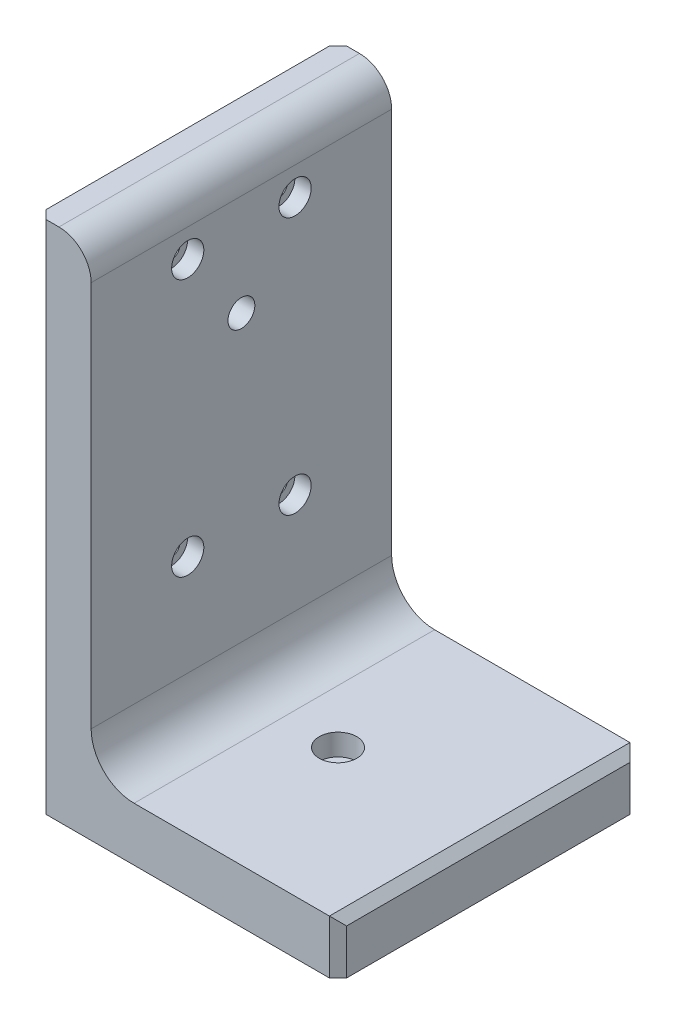
SolidWorks part; units mm, degrees
ref_plane "Plane1" through (0, 0, 0) normal (0, 0, 1) x (1, 0, 0)
ref_plane "Plane2" through (0, 0, 0) normal (0, 1, 0) x (1, 0, 0)
ref_plane "Plane3" through (0, 0, 0) normal (1, 0, 0) x (0, 0, -1)
extrude "BaseSteelAngle" add sketch "Sketch1" along normal mid plane 88.9
sketch "Sketch1" plane through (0, 0, 0) normal (0, 0, 1) x (1, 0, 0)
  line L0 (0, 0) -> (0, 152.4)
  line L1 (0, 152.4) -> (6.3551, 152.4)
  line L2 (15.875, 142.8801) -> (15.875, 28.575)
  line L3 (28.575, 15.875) -> (142.8801, 15.875)
  line L4 (152.4, 6.3551) -> (152.4, 0)
  line L5 (152.4, 0) -> (0, 0)
  arc A0 (152.4, 6.3551) -> (142.8801, 15.875) centre (142.8801, 6.3551) ccw
  arc A1 (6.3551, 152.4) -> (15.875, 142.8801) centre (6.3551, 142.8801) cw
  arc A2 (28.575, 15.875) -> (15.875, 28.575) centre (28.575, 28.575) cw
  circle A3 centre (0, 0) radius 9.525 construction
  dimension "D2" = 6.3551
  dimension "Radius_1" = 12.7
  dimension "Radius_2" = 9.525
  dimension "D1" = 15.875
  dimension "V_leg" = 152.4
  dimension "H_leg" = 152.4
  dimension "Thickness" = 15.875
  dimension "Flat_wid" = 6.3551
hole_wizard "#10-32 Tapped Hole1" positions "Sketch3" profile "Sketch2" tap size "#10-32" standard "Ansi Inch"
sketch "Sketch3" plane through (15.875, 0, 0) normal (1, 0, 0) x (0, 0, -1)
  point P0 (20.6375, 70.9295)
  point P1 (-20.6375, 70.9295)
  point P4 (-20.6375, 140.7795)
  point P7 (20.6375, 140.7795)
sketch "Sketch2" plane through (15.875, 70.9295, -20.6375) normal (0, 1, 0) x (0, 0, -1)
  line L0 (0, 0) -> (0, 15.875)
  line L1 (0, 15.875) -> (2.0193, 15.875)
  line L2 (2.0193, 15.875) -> (2.0193, 0)
  line L5 (2.0193, 0) -> (0, 0)
  line L11 (0, -6.35) -> (0, 107.95) construction
  dimension "Thru Tap Drill Dia." = 4.0386
  dimension "Thru Tap Drill Depth" = 15.875
cosmetic thread "Hole Thread1" [suppressed] parameters "D2"=4.826
cosmetic thread "Hole Thread2" [suppressed] parameters "D2"=4.826
cosmetic thread "Hole Thread3" [suppressed] parameters "D2"=4.826
cosmetic thread "Hole Thread4" [suppressed] parameters "D2"=4.826
hole_wizard "#10-32 Tapped Hole2" positions "Sketch5" profile "Sketch4" tap size "#10-32" standard "Ansi Inch"
sketch "Sketch5" plane through (0, 0, 0) normal (-1, 0, 0) x (0, 0, 1)
  point P0 (0, 7.9375)
  point P1 (0, 93.6625)
  dimension "D1" = 85.725
cosmetic thread "Hole Thread5" [suppressed] parameters "D1"=12.7, "D2"=4.826
cosmetic thread "Hole Thread6" [suppressed] parameters "D1"=12.7, "D2"=4.826
sketch "Sketch4" plane through (0, 7.9375, 0) normal (0, 1, 0) x (0, 0, 1)
  line L0 (0, 0) -> (0, 17.8757)
  line L1 (0, 17.8757) -> (2.0193, 16.6624)
  line L2 (2.0193, 16.6624) -> (2.0193, 0)
  line L5 (2.0193, 0) -> (0, 0)
  line L10 (0, 17.8757) -> (-2.0193, 16.6624) construction
  line L11 (0, -6.35) -> (0, 107.95) construction
  dimension "Tap Drill Dia." = 4.0386
  dimension "Tap Drill Depth" = 16.6624
  dimension "Drill Angle" = 118
hole_wizard "CBORE for #10 Socket Head Cap Screw1" positions "Sketch7" profile "Sketch6" counterbore size "#10" standard "Ansi Inch"
sketch "Sketch7" plane through (0, 0, 0) normal (0, -1, 0) x (1, 0, 0)
  point P0 (58.42, -15.875)
  point P3 (134.62, -15.875)
  point P6 (134.62, 15.875)
  point P9 (58.42, 15.875)
sketch "Sketch6" plane through (58.42, 0, -15.875) normal (1, 0, 0) x (0, 0, -1)
  line L0 (0, 0) -> (0, 152.4)
  line L1 (0, 152.4) -> (2.5527, 152.4)
  line L3 (2.5527, 152.4) -> (2.5527, 7.366)
  line L4 (2.5527, 7.366) -> (4.7625, 7.366)
  line L5 (4.7625, 7.366) -> (4.7625, 0)
  line L7 (4.7625, 0) -> (0, 0)
  line L11 (0, -6.35) -> (0, 107.95) construction
  dimension "Thru Hole Dia." = 5.1054
  dimension "Thru Hole Depth" = 152.4
  dimension "C'Bore Dia." = 9.525
  dimension "C'Bore Depth" = 7.366
hole_wizard "3/8-16 Tapped Hole1" positions "Sketch9" profile "Sketch8" tap size "3/8-16" standard "Ansi Inch" end condition through all
sketch "Sketch9" plane through (0, 0, 0) normal (-1, 0, 0) x (0, 0, 1)
  point P0 (0, 112.8903)
sketch "Sketch8" plane through (0, 112.8903, 0) normal (0, 1, 0) x (0, 0, 1)
  line L0 (0, 0) -> (0, 152.4)
  line L1 (0, 152.4) -> (3.9687, 152.4)
  line L2 (3.9687, 152.4) -> (3.9687, 0)
  line L5 (3.9687, 0) -> (0, 0)
  line L11 (0, -6.35) -> (0, 107.95) construction
  dimension "Thru Tap Drill Dia." = 7.9375
  dimension "Thru Tap Drill Depth" = 152.4
cosmetic thread "Hole Thread7" parameters "D2"=9.525
hole_wizard "CBORE for #10 Socket Head Cap Screw2" positions "Sketch11" profile "Sketch10" counterbore size "#10" standard "Ansi Inch" end condition through all
sketch "Sketch11" plane through (15.875, 58.1606, 30.4367) normal (-1, 0, 0) x (0, 0, 1)
  line L0 (-46.3117, 144.2702) -> (-46.3117, 50.4752) construction
  line L1 (-14.5617, 144.2702) -> (-14.5617, 50.4752) construction
  line L2 (-23.1841, 0.2594) -> (23.1841, 0.2594) construction
  line L3 (-23.1841, 76.4594) -> (23.1841, 76.4594) construction
  line L4 (-30.4367, 159.5145) -> (-30.4367, -13.4663) construction
  line L5 (14.0133, 94.2394) -> (-74.8867, 94.2394) construction
  point P0 (-46.3117, 0.2594)
  point P3 (-14.5617, 0.2594)
  point P6 (-14.5617, 76.4594)
  point P9 (-46.3117, 76.4594)
  dimension "D1" = 17.78
  dimension "D2" = 76.2
  dimension "D3" = 31.75
sketch "Sketch10" plane through (15.875, 58.42, -15.875) normal (0, 1, 0) x (0, 0, -1)
  line L0 (0, 0) -> (0, 15.875)
  line L1 (0, 15.875) -> (2.5527, 15.875)
  line L3 (2.5527, 15.875) -> (2.5527, 4.826)
  line L4 (2.5527, 4.826) -> (4.7625, 4.826)
  line L5 (4.7625, 4.826) -> (4.7625, 0)
  line L7 (4.7625, 0) -> (0, 0)
  line L11 (0, -6.35) -> (0, 107.95) construction
  dimension "Thru Hole Dia." = 5.1054
  dimension "Thru Hole Depth" = 15.875
  dimension "C'Bore Dia." = 9.525
  dimension "C'Bore Depth" = 4.826
sketch "Sketch16" plane through (0, 0, 0) normal (0, 1, 0) x (1, 0, 0)
  line L0 (0, -44.45) -> (119.1704, 74.7204) construction
  line L1 (88.9, 73.7036) -> (183.2089, 73.7036)
  line L2 (88.9, 73.7036) -> (88.9, -70.7977)
  line L3 (88.9, -70.7977) -> (183.2089, -70.7977)
  line L4 (183.2089, 73.7036) -> (183.2089, -70.7977)
  line L5 (142.8801, 44.45) -> (28.575, 44.45) construction
  point P9 (88.9, 44.45)
  dimension "D1" = 45
extrude "Cut-Extrude1" cut sketch "Sketch16" against normal mid plane 50.8
hole_wizard "#10-32 Tapped Hole3" positions "Sketch13" profile "Sketch12" tap size "#10-32" standard "Ansi Inch"
sketch "Sketch13" plane through (0, 0, 0) normal (-1, 0, 0) x (0, 0, 1)
  line L0 (-55.0425, 82.55) -> (65.2829, 82.55) construction
  line L1 (-62.3571, 19.05) -> (96.0043, 19.05) construction
  line L2 (-31.75, 124.9793) -> (-31.75, -6.318) construction
  line L3 (31.75, 124.2936) -> (31.75, -7.0037) construction
  line L4 (0, 145.8717) -> (0, -4.4436) construction
  line L5 (44.45, 0) -> (-44.45, 0) construction
  point P0 (-31.75, 82.55)
  point P11 (31.75, 82.55)
  point P13 (31.75, 19.05)
  point P15 (-31.75, 19.05)
  dimension "D1" = 19.05
  dimension "D2" = 63.5
  dimension "D3" = 63.5
sketch "Sketch12" plane through (0, 82.55, -31.75) normal (0, 1, 0) x (0, 0, 1)
  line L0 (0, 0) -> (0, 14.8277)
  line L1 (0, 14.8277) -> (2.0193, 13.6144)
  line L2 (2.0193, 13.6144) -> (2.0193, 0)
  line L5 (2.0193, 0) -> (0, 0)
  line L10 (0, 14.8277) -> (-2.0193, 13.6144) construction
  line L11 (0, -6.35) -> (0, 107.95) construction
  dimension "Tap Drill Dia." = 4.0386
  dimension "Tap Drill Depth" = 13.6144
  dimension "Drill Angle" = 118
cosmetic thread "Hole Thread8" parameters "D1"=9.652, "D2"=4.826
cosmetic thread "Hole Thread9" parameters "D1"=9.652, "D2"=4.826
cosmetic thread "Hole Thread10" parameters "D1"=9.652, "D2"=4.826
cosmetic thread "Hole Thread11" parameters "D1"=9.652, "D2"=4.826
hole_wizard "#10-32 Tapped Hole4" positions "Sketch15" profile "Sketch14" tap size "#10-32" standard "Ansi Inch"
sketch "Sketch15" plane through (0, 0, 0) normal (0, -1, 0) x (1, 0, 0)
  line L0 (-15.7314, -31.75) -> (164.433, -31.75) construction
  line L1 (-17.5806, 31.75) -> (173.6789, 31.75) construction
  line L3 (76.2, -68.0239) -> (76.2, 68.5523) construction
  line L4 (12.7, -80.1758) -> (12.7, 68.5523) construction
  line L5 (-6.4854, 0) -> (173.6789, 0) construction
  line L6 (0, 44.45) -> (0, -44.45) construction
  point P14 (76.2, 31.75)
  point P16 (12.7, 31.75)
  point P18 (12.7, -31.75)
  point P20 (76.2, -31.75)
  dimension "D1" = 63.5
  dimension "D2" = 12.7
  dimension "D3" = 63.5
sketch "Sketch14" plane through (76.2, 0, 31.75) normal (1, 0, 0) x (0, 0, -1)
  line L0 (0, 0) -> (0, 14.8277)
  line L1 (0, 14.8277) -> (2.0193, 13.6144)
  line L2 (2.0193, 13.6144) -> (2.0193, 0)
  line L5 (2.0193, 0) -> (0, 0)
  line L10 (0, 14.8277) -> (-2.0193, 13.6144) construction
  line L11 (0, -6.35) -> (0, 107.95) construction
  dimension "Tap Drill Dia." = 4.0386
  dimension "Tap Drill Depth" = 13.6144
  dimension "Drill Angle" = 118
cosmetic thread "Hole Thread18" parameters "D1"=9.652, "D2"=4.826
cosmetic thread "Hole Thread19" parameters "D1"=9.652, "D2"=4.826
cosmetic thread "Hole Thread20" parameters "D1"=9.652, "D2"=4.826
cosmetic thread "Hole Thread21" parameters "D1"=9.652, "D2"=4.826
hole_wizard "CBORE for 1/4 Socket Head Cap Screw1" positions "Sketch18" profile "Sketch17" counterbore size "1/4" standard "Ansi Inch" end condition through all
sketch "Sketch18" plane through (0, 15.875, 0) normal (0, 1, 0) x (-1, 0, 0)
  line L0 (0, 44.45) -> (-88.9, -44.45) construction
  point P0 (-44.45, 0)
sketch "Sketch17" plane through (44.45, 15.875, 0) normal (1, 0, 0) x (0, 0, 1)
  line L0 (0, 0) -> (0, 15.875)
  line L1 (0, 15.875) -> (3.3782, 15.875)
  line L3 (3.3782, 15.875) -> (3.3782, 6.35)
  line L4 (3.3782, 6.35) -> (5.5562, 6.35)
  line L5 (5.5562, 6.35) -> (5.5563, 0)
  line L7 (5.5563, 0) -> (0, 0)
  line L11 (0, -6.35) -> (0, 107.95) construction
  dimension "Thru Hole Dia." = 6.7564
  dimension "Thru Hole Depth" = 15.875
  dimension "C'Bore Dia." = 11.1125
  dimension "C'Bore Depth" = 6.35
sketch "Sketch19" plane through (0, 0, 0) normal (0, -1, 0) x (1, 0, 0)
  circle A0 centre (44.45, 0) radius 25.4
  dimension "D1" = 50.8
extrude "Cut-Extrude2" cut sketch "Sketch19" against normal blind 0.508
chamfer "Chamfer1" distance 2.54 angle 45 5 edges at (88.9, 7.9375, 44.45) (88.9, 7.9375, -44.45) (88.9, 15.875, 0) (0, 76.2, -44.45) (0, 76.2, 44.45)
equation "\"Flat_wid@Sketch1\" = ((sgn(\"Thickness@Sketch1\" - \"Radius_2@Sketch1\") +1)*(\"Thickness@Sketch1\" - \"Radius_2@Sketch1\"))/2 +0.0002"
equation "\"D1@Sketch1\" = \"Thickness@Sketch1\""
equation "\"D2@Sketch1\" = \"Flat_wid@Sketch1\""
